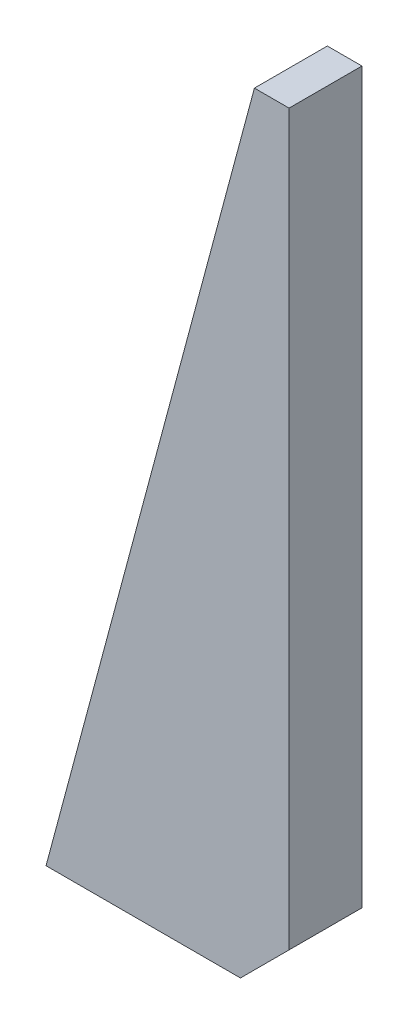
SolidWorks part; units mm, degrees
ref_plane "Front Plane" through (0, 0, 0) normal (0, 0, 1) x (1, 0, 0)
ref_plane "Top Plane" through (0, 0, 0) normal (0, 1, 0) x (1, 0, 0)
ref_plane "Right Plane" through (0, 0, 0) normal (1, 0, 0) x (0, 0, -1)
sketch "Sketch1" plane through (0, 0, 0) normal (0, 0, 1) x (1, 0, 0)
  line L0 (0, 80) -> (0, -70)
  line L1 (-10, -80) -> (-50, -80)
  line L2 (-50, -80) -> (-7.1281, 80)
  line L3 (0, 80) -> (-7.1281, 80)
  line L4 (0, -70) -> (-10, -80)
  point P1 (0, -80)
  point P4 (0, 0)
extrude "Boss-Extrude1" add sketch "Sketch1" along normal mid plane 15
